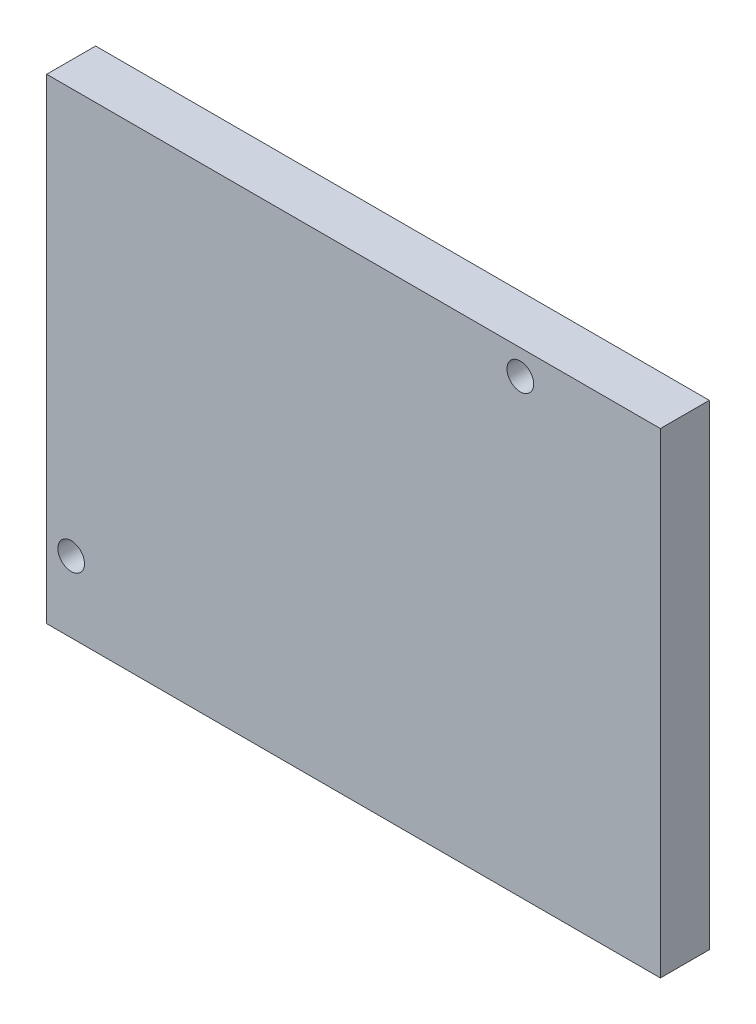
SolidWorks part; units mm, degrees
ref_plane "Front Plane" through (0, 0, 0) normal (0, 0, 1) x (1, 0, 0)
ref_plane "Top Plane" through (0, 0, 0) normal (0, 1, 0) x (1, 0, 0)
ref_plane "Right Plane" through (0, 0, 0) normal (1, 0, 0) x (0, 0, -1)
sketch "Sketch1" plane through (0, 0, 0) normal (0, 0, 1) x (1, 0, 0)
  line L1 (-34.5, -26.75) -> (34.5, -26.75)
  line L2 (-34.5, -26.75) -> (-34.5, 26.75)
  line L3 (-34.5, 26.75) -> (34.5, 26.75)
  line L4 (34.5, -26.75) -> (34.5, 26.75)
  line L5 (-34.5, -26.75) -> (34.5, 26.75) construction
  line L6 (-34.5, 26.75) -> (34.5, -26.75) construction
  circle A0 centre (18.75, 23.95) radius 1.5
  circle A1 centre (-31.75, -18.79) radius 1.5
  point P0 (0, 0)
  dimension "D5" = 3
  dimension "D8" = 3
  dimension "D1" = 69
  dimension "D2" = 53.5
  dimension "D3" = 15.75
  dimension "D4" = 2.8
  dimension "D6" = 7.96
  dimension "D7" = 2.75
extrude "Boss-Extrude1" add sketch "Sketch1" along normal blind 5.5
equation "\"D1@Boss-Extrude1\"=\"mat@V1.assembly\""
